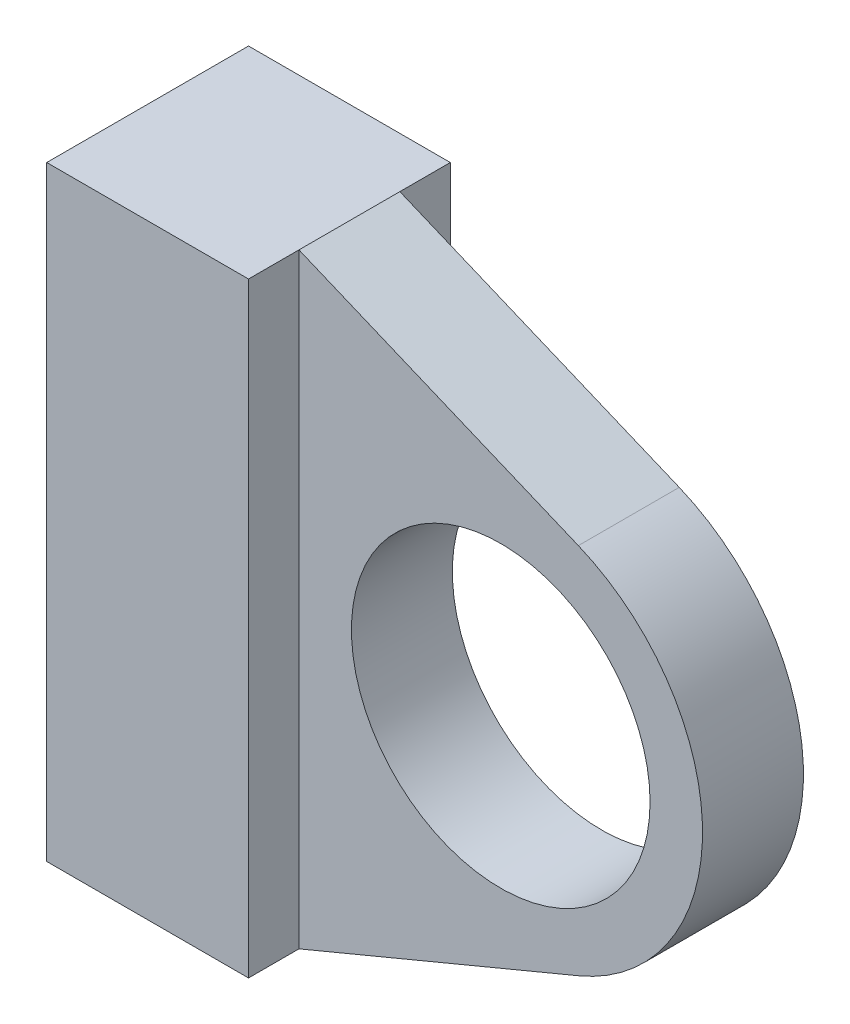
SolidWorks part; units mm, degrees
ref_plane "Front" through (0, 0, 0) normal (0, 0, 1) x (1, 0, 0)
ref_plane "Top" through (0, 0, 0) normal (0, 1, 0) x (1, 0, 0)
ref_plane "Right" through (0, 0, 0) normal (1, 0, 0) x (0, 0, -1)
sketch "Sketch1" plane through (0, 0, 0) normal (0, 0, 1) x (1, 0, 0)
  line L0 (-601.4273, -1564.5503) -> (-601.4273, -1602.6503)
  line L1 (-601.4273, -1564.5503) -> (-588.7273, -1564.5503)
  line L2 (-601.4273, -1602.6503) -> (-588.7273, -1602.6503)
  line L3 (-588.7273, -1602.6503) -> (-601.4273, -1602.6503) construction
  line L4 (-588.7273, -1564.5503) -> (-601.4273, -1564.5503) construction
  line L5 (-588.7273, -1564.5503) -> (-571.1427, -1571.8773)
  line L6 (-588.7273, -1602.6503) -> (-571.1427, -1595.3234)
  arc A0 (-571.1427, -1571.8773) -> (-571.1427, -1595.3234) centre (-576.0273, -1583.6003) ccw construction
  arc A1 (-571.1427, -1595.3234) -> (-571.1427, -1571.8773) centre (-576.0273, -1583.6003) ccw
  circle A2 centre (-576.0273, -1583.6003) radius 9.398
  dimension "D1" = 25.4
  dimension "D2" = 18.796
extrude "Boss-Extrude1" add sketch "Sketch1" along normal mid plane 6.35
sketch "Sketch2" plane through (0, 0, 0) normal (0, 0, 1) x (1, 0, 0)
  line L1 (-601.4273, -1564.5503) -> (-588.7273, -1564.5503)
  line L2 (-601.4273, -1564.5503) -> (-601.4273, -1602.6503)
  line L3 (-601.4273, -1602.6503) -> (-588.7273, -1602.6503)
  line L4 (-588.7273, -1564.5503) -> (-588.7273, -1602.6503)
extrude "Boss-Extrude2" add sketch "Sketch2" along normal mid plane 12.7
